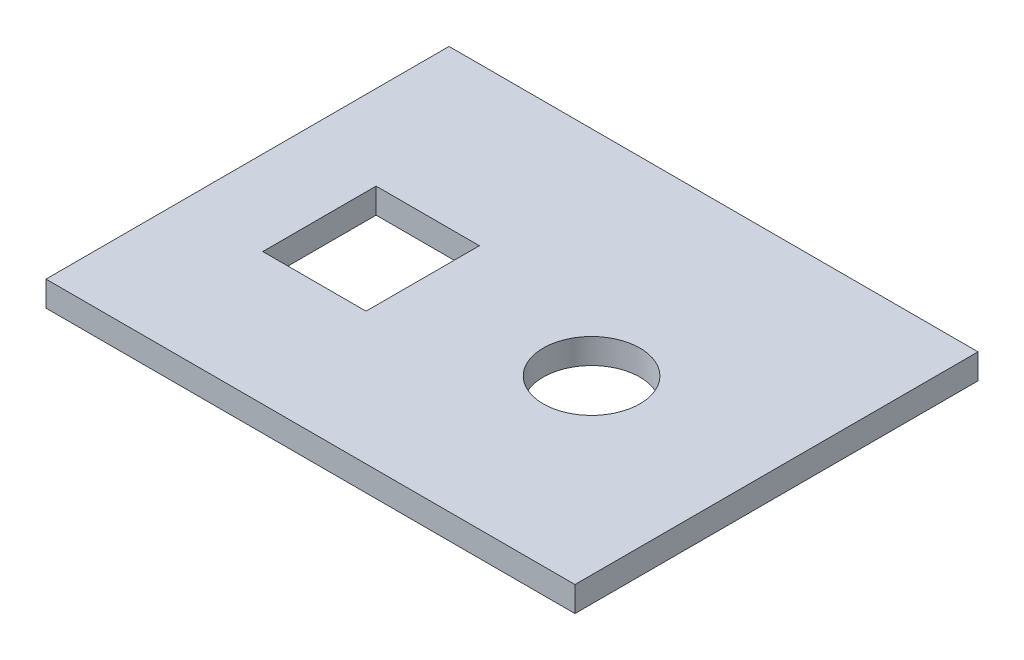
SolidWorks part; units mm, degrees
ref_plane "Front Plane" through (0, 0, 0) normal (0, 0, 1) x (1, 0, 0)
ref_plane "Top Plane" through (0, 0, 0) normal (0, 1, 0) x (1, 0, 0)
ref_plane "Right Plane" through (0, 0, 0) normal (1, 0, 0) x (0, 0, -1)
sketch "Sketch2" plane through (0, 0, 0) normal (0, 1, 0) x (1, 0, 0)
  line L1 (110, 85) -> (-100, 85)
  line L2 (110, 85) -> (110, -75)
  line L3 (110, -75) -> (-100, -75)
  line L4 (-100, 85) -> (-100, -75)
  line L5 (110, 85) -> (-100, -75) construction
  line L6 (110, -75) -> (-100, 85) construction
  point P0 (5, 5)
  dimension "D1" = 160
  dimension "D2" = 210
extrude "Boss-Extrude1" add sketch "Sketch2" along normal blind 10 contours L4 L3 L2 L1
sketch "Sketch3" plane through (0, 0, 0) normal (0, 1, 0) x (1, 0, 0)
  line L0 (0, 0) -> (22.385, 0) construction
  line L1 (0, 0) -> (-25.4527, 0) construction
  line L6 (-66.4527, -22.5) -> (-25.4527, -22.5)
  line L7 (-66.4527, -22.5) -> (-66.4527, 22.5)
  line L8 (-25.4527, -22.5) -> (-25.4527, 22.5)
  line L9 (-66.4527, 22.5) -> (-25.4527, 22.5)
  line L10 (-66.4527, -22.5) -> (-25.4527, 22.5) construction
  line L11 (-25.4527, -22.5) -> (-66.4527, 22.5) construction
  circle A1 centre (41.585, 0) radius 19.2
  point P6 (0, 0)
  point P7 (-45.9527, 0)
  dimension "D1" = 38.4
  dimension "D2" = 41
  dimension "D3" = 45
extrude "Cut-Extrude2" cut sketch "Sketch3" against normal blind 22 and the other way blind 15
